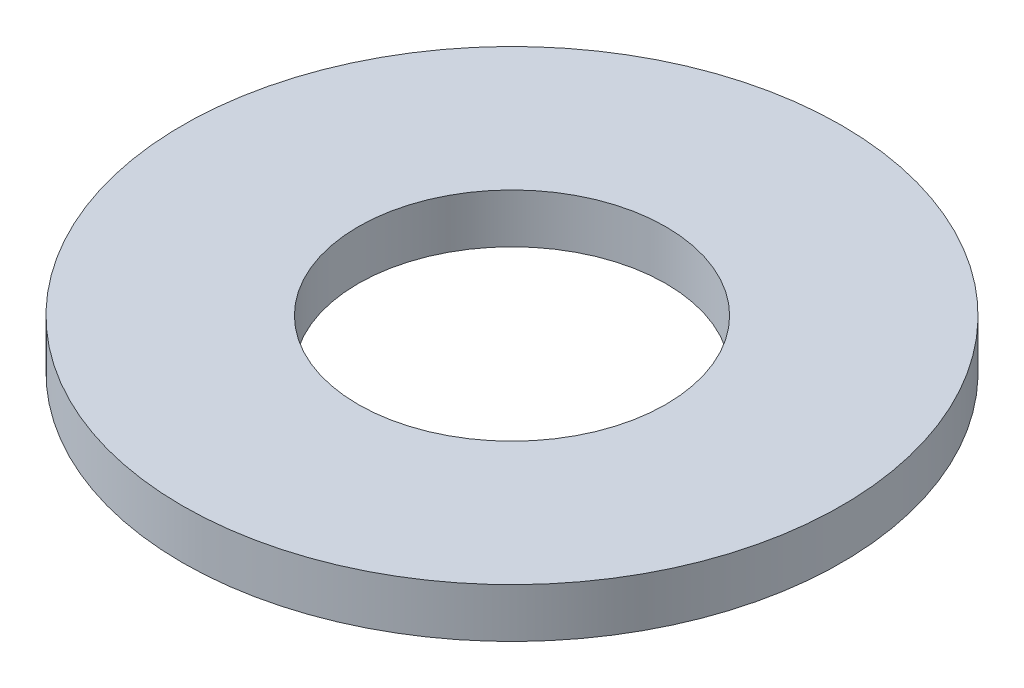
SolidWorks part; units mm, degrees
ref_plane "Front Plane" through (0, 0, 0) normal (0, 0, 1) x (1, 0, 0)
ref_plane "Top Plane" through (0, 0, 0) normal (0, 1, 0) x (1, 0, 0)
ref_plane "Right Plane" through (0, 0, 0) normal (1, 0, 0) x (0, 0, -1)
sketch "Sketch2" plane through (0, 0, 0) normal (0, 1, 0) x (1, 0, 0)
  circle A0 centre (0, 0) radius 3.48
  circle A1 centre (0, 0) radius 1.625
  dimension "D1" = 6.96
  dimension "D2" = 3.25
extrude "Boss-Extrude1" add sketch "Sketch2" along normal blind 0.52
